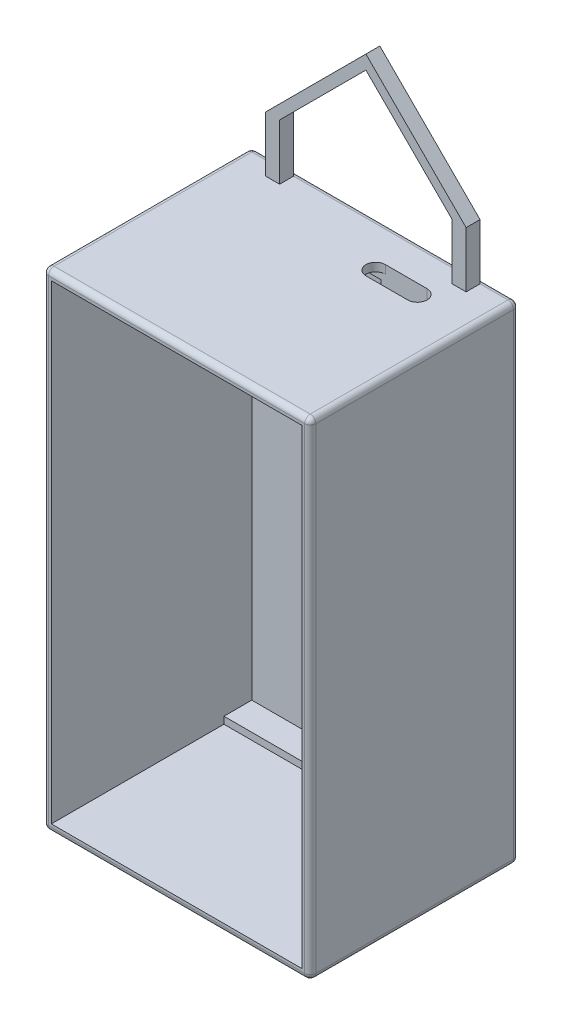
SolidWorks part; units mm, degrees
ref_plane "Front Plane" through (0, 0, 0) normal (0, 0, 1) x (1, 0, 0)
ref_plane "Top Plane" through (0, 0, 0) normal (0, 1, 0) x (1, 0, 0)
ref_plane "Right Plane" through (0, 0, 0) normal (1, 0, 0) x (0, 0, -1)
sketch "Sketch1" plane through (0, 0, 0) normal (0, 0, 1) x (1, 0, 0)
  line L1 (48, 87.5) -> (-48, 87.5)
  line L2 (48, 87.5) -> (48, -87.5)
  line L3 (48, -87.5) -> (-48, -87.5)
  line L4 (-48, 87.5) -> (-48, -87.5)
  line L5 (48, 87.5) -> (-48, -87.5) construction
  line L6 (48, -87.5) -> (-48, 87.5) construction
  point P0 (0, 0)
  dimension "D1" = 175
  dimension "D2" = 96
extrude "Boss-Extrude1" add sketch "Sketch1" along normal blind 100
sketch "Sketch2" plane through (0, 0, 100) normal (0, 0, 1) x (1, 0, 0)
  line L0 (-48, 87.5) -> (-48, -87.5) construction
  line L1 (45, 84.5) -> (-45, 84.5)
  line L2 (45, 84.5) -> (45, -84.5)
  line L3 (45, -84.5) -> (-45, -84.5)
  line L4 (-45, 84.5) -> (-45, -84.5)
  line L5 (45, 84.5) -> (-45, -84.5) construction
  line L6 (45, -84.5) -> (-45, 84.5) construction
  line L8 (-48, -87.5) -> (48, -87.5) construction
  point P0 (0, 0)
  dimension "D1" = 3
  dimension "D2" = 3
extrude "Cut-Extrude1" cut sketch "Sketch2" against normal blind 87
sketch "Sketch3" plane through (0, 0, 13) normal (0, 0, 1) x (1, 0, 0)
  line L0 (-45, 84.5) -> (-45, -84.5) construction
  line L1 (-45, 82) -> (11.5, 82)
  line L2 (-45, 82) -> (-45, -82)
  line L3 (-45, -82) -> (11.5, -82)
  line L4 (11.5, 82) -> (11.5, -82)
  line L5 (-45, -84.5) -> (45, -84.5) construction
  line L6 (45, 84.5) -> (-45, 84.5) construction
  dimension "D1" = 2.5
  dimension "D2" = 2.5
  dimension "D3" = 56.5
extrude "Cut-Extrude2" cut sketch "Sketch3" against normal blind 10
sketch "Sketch4" plane through (0, 0, 13) normal (0, 0, 1) x (1, 0, 0)
  line L0 (11.5, -72.6234) -> (45, -72.6234) construction
  line L1 (11.5, -82) -> (11.5, 82) construction
  line L2 (45, -84.5) -> (45, 84.5) construction
  line L3 (28.25, -72.6234) -> (28.25, -84.5) construction
  line L4 (-45, -84.5) -> (45, -84.5) construction
sketch "Sketch5" plane through (0, -84.5, 0) normal (0, 1, 0) x (1, 0, 0)
  line L0 (28.25, -13) -> (28.25, -23) construction
  circle A0 centre (28.25, -23) radius 6
  dimension "D2" = 12
  dimension "D1" = 10
extrude "Cut-Extrude3" cut sketch "Sketch5" against normal blind 10
sketch "Sketch6" plane through (0, 0, 13) normal (0, 0, 1) x (1, 0, 0)
  line L0 (45, -84.5) -> (45, 84.5) construction
  line L1 (28.25, -84.5) -> (28.25, -39.5) construction
  line L2 (45, -39.5) -> (11.5, -39.5)
  line L3 (45, -39.5) -> (45, 8.5)
  line L4 (45, 8.5) -> (11.5, 8.5)
  line L5 (11.5, -39.5) -> (11.5, 8.5)
  line L6 (11.5, -82) -> (11.5, 82) construction
  dimension "D1" = 45
  dimension "D2" = 48
extrude "Cut-Extrude4" cut sketch "Sketch6" against normal blind 10
sketch "Sketch7" plane through (0, 0, 13) normal (0, 0, 1) x (1, 0, 0)
  line L0 (45, 84.5) -> (13, 84.5) construction
  line L1 (45, 84.5) -> (-45, 84.5) construction
  dimension "D1" = 32
sketch "Sketch9" plane through (0, 84.5, 0) normal (0, -1, 0) x (1, 0, 0)
  line L0 (13, 13) -> (13, 16.5) construction
  line L1 (13, 16.5) -> (28, 16.5) construction
  line L2 (13, 20) -> (28, 20)
  line L3 (13, 13) -> (28, 13)
  arc A0 (13, 20) -> (13, 13) centre (13, 16.5) ccw
  arc A1 (28, 13) -> (28, 20) centre (28, 16.5) ccw
  point P3 (20.5, 16.5)
  dimension "D1" = 3.5
  dimension "D2" = 15
  dimension "D3" = 7
extrude "Cut-Extrude6" cut sketch "Sketch9" against normal blind 10
sketch "Sketch10" plane through (0, -87.5, 0) normal (0, -1, 0) x (1, 0, 0)
  line L0 (48, 100) -> (48, 0) construction
  line L1 (-48, 100) -> (48, 100)
  line L2 (-48, 100) -> (-48, 75)
  line L3 (-48, 75) -> (48, 75)
  line L4 (48, 100) -> (48, 75)
  dimension "D1" = 25
extrude "Cut-Extrude8" cut sketch "Sketch10" against normal blind 200
fillet "Fillet1" radius 2 12 edges at (0, 87.5, 0) (0, 87.5, 75) (48, 87.5, 37.5) (48, 0, 0) (48, 0, 75) (-48, 87.5, 37.5) (-48, 0, 75) (-48, 0, 0) (0, -87.5, 75) (48, -87.5, 37.5) (0, -87.5, 0) (-48, -87.5, 37.5)
sketch "Sketch11" plane through (0, -87.5, 0) normal (0, -1, 0) x (1, 0, 0)
  line L0 (28.25, 23) -> (0, 23) construction
  circle A0 centre (0, 23) radius 2.5
  dimension "D1" = 5
extrude "Cut-Extrude9" cut sketch "Sketch11" against normal blind 5
sketch "Sketch12" plane through (0, 87.5, 0) normal (0, 1, 0) x (1, 0, 0)
  line L0 (-46, -2) -> (-46, -73) construction
  line L1 (-36, -2) -> (-31, -2)
  line L2 (-36, -2) -> (-36, -7)
  line L3 (-36, -7) -> (-31, -7)
  line L4 (-31, -2) -> (-31, -7)
  line L5 (-36, -2) -> (-31, -7) construction
  line L6 (-36, -7) -> (-31, -2) construction
  line L7 (46, -2) -> (-46, -2) construction
  line L8 (0, -2) -> (0, -73) construction
  line L9 (-46, -73) -> (46, -73) construction
  line L10 (36, -7) -> (31, -2) construction
  line L11 (36, -2) -> (31, -7) construction
  line L12 (31, -2) -> (31, -7)
  line L13 (36, -7) -> (31, -7)
  line L14 (36, -2) -> (36, -7)
  line L15 (36, -2) -> (31, -2)
  point P0 (-33.5, -4.5)
  point P17 (33.5, -4.5)
  dimension "D1" = 10
  dimension "D2" = 5
  dimension "D3" = 5
  dimension "D4" = 0
extrude "Boss-Extrude2" add sketch "Sketch12" along normal blind 20
sketch "Sketch15" plane through (0, 0, 7) normal (0, 0, 1) x (1, 0, 0)
  line L0 (-31, 107.5) -> (0, 138.5)
  line L1 (0, 138.5) -> (31, 107.5)
  line L2 (31, 107.5) -> (36, 107.5)
  line L3 (36, 107.5) -> (0, 143.5)
  line L4 (0, 143.5) -> (-36, 107.5)
  line L5 (-36, 107.5) -> (-31, 107.5)
extrude "Boss-Extrude5" add sketch "Sketch15" against normal blind 5
